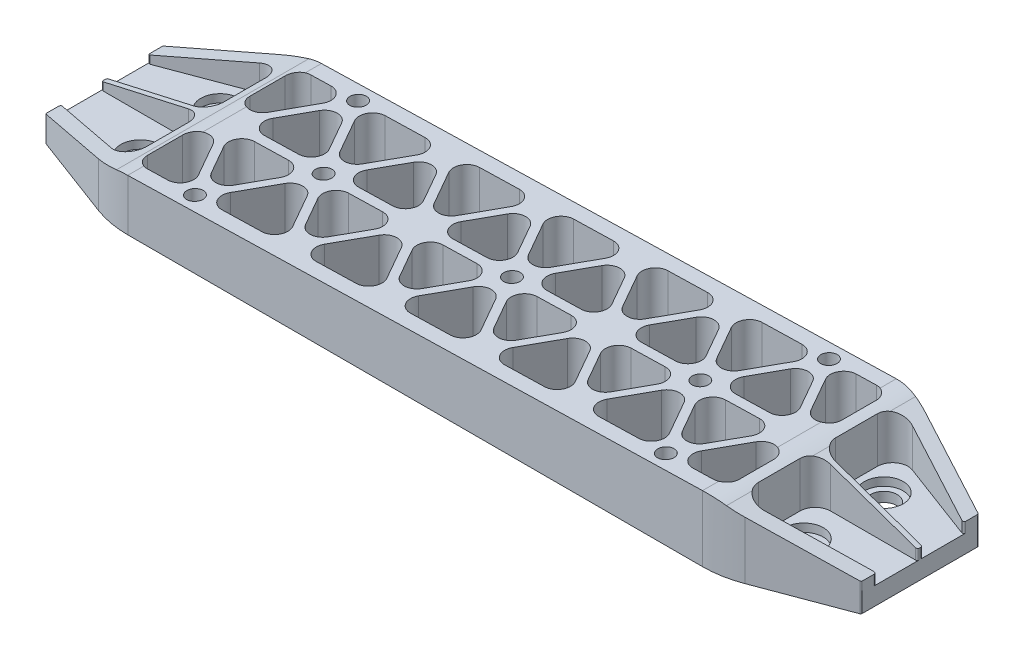
SolidWorks part; units mm, degrees
ref_plane "Front Plane" through (0, 0, 0) normal (0, 0, 1) x (1, 0, 0)
ref_plane "Top Plane" through (0, 0, 0) normal (0, 1, 0) x (1, 0, 0)
ref_plane "Right Plane" through (0, 0, 0) normal (1, 0, 0) x (0, 0, -1)
sketch "Sketch1" plane through (0, 0, 0) normal (0, 1, 0) x (1, 0, 0)
  line L0 (25.4, 0) -> (177.8, 0)
  line L1 (177.8, 0) -> (203.2, -9.525)
  line L2 (203.2, -9.525) -> (203.2, -38.735)
  line L3 (203.2, -38.735) -> (177.8, -48.26)
  line L4 (177.8, -48.26) -> (25.4, -48.26)
  line L5 (25.4, -48.26) -> (0, -38.735)
  line L6 (0, -38.735) -> (0, -9.525)
  line L7 (0, -9.525) -> (25.4, 0)
  line L8 (0, -9.525) -> (203.2, -9.525) construction
  line L9 (25.4, 0) -> (25.4, -48.26) construction
  dimension "D1" = 25.4
  dimension "D2" = 9.525
  dimension "D3" = 177.8
  dimension "D4" = 203.2
  dimension "D5" = 38.735
  dimension "D6" = 48.26
extrude "Boss-Extrude1" add sketch "Sketch1" against normal blind 17.1704
sketch "Sketch2" plane through (0, -17.1704, 0) normal (0, -1, 0) x (1, 0, 0)
  line L0 (0, 24.13) -> (203.2, 24.13) construction
  line L1 (0, 9.525) -> (0, 38.735) construction
  line L2 (203.2, 38.735) -> (203.2, 9.525) construction
  circle A0 centre (54.6608, 24.13) radius 3.4925
  circle A1 centre (101.6, 24.13) radius 3.4925
  circle A2 centre (148.5392, 24.13) radius 3.4925
  dimension "D2" = 6.985
  dimension "D1" = 24.13
  dimension "D3" = 54.6608
  dimension "D4" = 101.6
  dimension "D5" = 148.5392
extrude "Boss-Extrude2" add sketch "Sketch2" along normal blind 5.08
fillet "Fillet1" radius 25.4 4 edges at (177.8, -8.5852, 48.26) (25.4, -8.5852, 48.26) (177.8, -8.5852, 0) (25.4, -8.5852, 0)
fillet "Fillet2" radius 0.381 4 edges at (203.2, -8.5852, 38.735) (203.2, -8.5852, 9.525) (0, -8.5852, 9.525) (0, -8.5852, 38.735)
sketch "Sketch3" plane through (0, 0, 0) normal (0, 1, 0) x (1, 0, 0)
  line L0 (27.94, -24.13) -> (175.26, -24.13) construction
  line L1 (27.94, -3.81) -> (175.26, -3.81) construction
  line L2 (27.94, -3.81) -> (27.94, -44.45) construction
  line L3 (27.94, -44.45) -> (175.26, -44.45) construction
  line L4 (175.26, -3.81) -> (175.26, -44.45) construction
  line L5 (42.929, -3.81) -> (66.3926, -44.45) construction
  line L6 (78.1243, -24.13) -> (66.3926, -3.81) construction
  line L7 (66.3926, -3.81) -> (42.929, -3.81) construction
  line L8 (42.929, -3.81) -> (31.1973, -24.13) construction
  line L9 (31.1973, -24.13) -> (42.929, -44.45) construction
  line L10 (42.929, -44.45) -> (66.3926, -44.45) construction
  line L11 (66.3926, -44.45) -> (78.1243, -24.13) construction
  line L12 (125.0513, -24.13) -> (113.3196, -3.81) construction
  line L13 (113.3196, -3.81) -> (89.8561, -3.81) construction
  line L14 (89.8561, -3.81) -> (78.1243, -24.13) construction
  line L15 (78.1243, -24.13) -> (89.8561, -44.45) construction
  line L16 (89.8561, -44.45) -> (113.3196, -44.45) construction
  line L17 (113.3196, -44.45) -> (125.0513, -24.13) construction
  line L18 (160.2466, -3.81) -> (136.7831, -3.81) construction
  line L19 (136.7831, -3.81) -> (125.0513, -24.13) construction
  line L20 (125.0513, -24.13) -> (136.7831, -44.45) construction
  line L21 (136.7831, -44.45) -> (160.2466, -44.45) construction
  line L22 (160.2466, -44.45) -> (171.9784, -24.13) construction
  line L23 (171.9784, -24.13) -> (160.2466, -3.81) construction
  line L24 (42.929, -44.45) -> (66.3926, -3.81) construction
  line L28 (57.4544, -31.0007) -> (62.4258, -39.6113)
  line L29 (59.6321, -44.45) -> (49.6895, -44.45)
  line L30 (46.8958, -39.6113) -> (51.8672, -31.0007)
  line L31 (38.6909, -25.4) -> (47.1671, -25.4)
  line L32 (49.9608, -30.2387) -> (45.7227, -37.5793)
  line L33 (40.1354, -37.5793) -> (35.8973, -30.2387)
  line L34 (40.1354, -10.6807) -> (35.8973, -18.0213)
  line L35 (49.9608, -18.0213) -> (45.7227, -10.6807)
  line L36 (38.6909, -22.86) -> (47.1671, -22.86)
  line L37 (46.8958, -8.6487) -> (51.8672, -17.2593)
  line L38 (59.6321, -3.81) -> (49.6895, -3.81)
  line L39 (57.4544, -17.2593) -> (62.4258, -8.6487)
  line L40 (63.605, -37.5793) -> (59.3669, -30.2387)
  line L41 (62.1605, -25.4) -> (70.6367, -25.4)
  line L42 (70.3654, -39.6113) -> (75.3368, -31.0007)
  line L43 (73.4304, -30.2387) -> (69.1923, -37.5793)
  line L44 (80.924, -31.0007) -> (85.8954, -39.6113)
  line L45 (83.1017, -44.45) -> (73.1591, -44.45)
  line L46 (70.3654, -8.6487) -> (75.3368, -17.2593)
  line L47 (83.1017, -3.81) -> (73.1591, -3.81)
  line L48 (80.924, -17.2593) -> (85.8954, -8.6487)
  line L49 (63.605, -10.6807) -> (59.3669, -18.0213)
  line L50 (73.4304, -18.0213) -> (69.1923, -10.6807)
  line L51 (62.1605, -22.86) -> (70.6367, -22.86)
  line L52 (87.0746, -37.5793) -> (82.8365, -30.2387)
  line L53 (85.6301, -25.4) -> (94.1063, -25.4)
  line L54 (93.835, -39.6113) -> (98.8064, -31.0007)
  line L55 (96.9, -30.2387) -> (92.6619, -37.5793)
  line L56 (104.3936, -31.0007) -> (109.365, -39.6113)
  line L57 (106.5713, -44.45) -> (96.6287, -44.45)
  line L58 (93.835, -8.6487) -> (98.8064, -17.2593)
  line L59 (106.5713, -3.81) -> (96.6287, -3.81)
  line L60 (104.3936, -17.2593) -> (109.365, -8.6487)
  line L61 (87.0746, -10.6807) -> (82.8365, -18.0213)
  line L62 (96.9, -18.0213) -> (92.6619, -10.6807)
  line L63 (85.6301, -22.86) -> (94.1063, -22.86)
  line L64 (110.5442, -37.5793) -> (106.3061, -30.2387)
  line L65 (109.0997, -25.4) -> (117.5759, -25.4)
  line L66 (117.3046, -39.6113) -> (122.276, -31.0007)
  line L67 (120.3696, -30.2387) -> (116.1315, -37.5793)
  line L68 (127.8632, -31.0007) -> (132.8346, -39.6113)
  line L69 (130.0409, -44.45) -> (120.0983, -44.45)
  line L70 (117.3046, -8.6487) -> (122.276, -17.2593)
  line L71 (130.0409, -3.81) -> (120.0983, -3.81)
  line L72 (127.8632, -17.2593) -> (132.8346, -8.6487)
  line L73 (110.5442, -10.6807) -> (106.3061, -18.0213)
  line L74 (120.3696, -18.0213) -> (116.1315, -10.6807)
  line L75 (109.0997, -22.86) -> (117.5759, -22.86)
  line L76 (134.0138, -37.5793) -> (129.7757, -30.2387)
  line L77 (132.5693, -25.4) -> (141.0455, -25.4)
  line L78 (140.7742, -39.6113) -> (145.7456, -31.0007)
  line L79 (143.8392, -30.2387) -> (139.6011, -37.5793)
  line L80 (151.3328, -31.0007) -> (156.3042, -39.6113)
  line L81 (153.5105, -44.45) -> (143.5679, -44.45)
  line L82 (140.7742, -8.6487) -> (145.7456, -17.2593)
  line L83 (153.5105, -3.81) -> (143.5679, -3.81)
  line L84 (151.3328, -17.2593) -> (156.3042, -8.6487)
  line L85 (134.0138, -10.6807) -> (129.7757, -18.0213)
  line L86 (143.8392, -18.0213) -> (139.6011, -10.6807)
  line L87 (132.5693, -22.86) -> (141.0455, -22.86)
  line L88 (157.4834, -37.5793) -> (153.2453, -30.2387)
  line L89 (156.0389, -25.4) -> (164.5151, -25.4)
  line L90 (164.2438, -39.6113) -> (169.2406, -30.9567)
  line L91 (167.3088, -30.2387) -> (163.0707, -37.5793)
  line L94 (164.2438, -8.6487) -> (169.2406, -17.3033)
  line L97 (157.4834, -10.6807) -> (153.2453, -18.0213)
  line L98 (167.3088, -18.0213) -> (163.0707, -10.6807)
  line L99 (156.0389, -22.86) -> (164.5151, -22.86)
  line L101 (33.9594, -30.9567) -> (38.9562, -39.6113)
  line L105 (33.9594, -17.3033) -> (38.9562, -8.6487)
  line L106 (23.4262, -39.6113) -> (28.3976, -31.0007) [skipped]
  line L107 (23.4262, -8.6487) -> (28.3976, -17.2593) [skipped]
  line L108 (36.1625, -3.81) -> (26.2199, -3.81) [skipped]
  line L109 (36.1625, -44.45) -> (26.2199, -44.45) [skipped]
  line L110 (174.8024, -17.2593) -> (179.7738, -8.6487) [skipped]
  line L111 (176.9801, -3.81) -> (167.0375, -3.81) [skipped]
  line L112 (174.8024, -31.0007) -> (179.7738, -39.6113) [skipped]
  line L113 (176.9801, -44.45) -> (167.0375, -44.45) [skipped]
  line L114 (27.94, -7.0358) -> (27.94, -15.6904)
  line L115 (27.94, -32.5696) -> (27.94, -41.2242)
  line L116 (175.26, -32.5696) -> (175.26, -41.2242)
  line L117 (175.26, -7.0358) -> (175.26, -15.6904)
  line L118 (167.0375, -44.45) -> (172.0342, -44.45)
  line L119 (167.0375, -3.81) -> (172.0342, -3.81)
  line L120 (36.1625, -3.81) -> (31.1658, -3.81)
  line L121 (36.1625, -44.45) -> (31.1658, -44.45)
  line L122 (203.2, -38.471) -> (203.2, -9.789) construction
  line L123 (173.1941, 0) -> (30.0059, 0) construction
  circle A0 centre (54.6608, -24.13) radius 20.32 construction
  circle A1 centre (101.5878, -24.13) radius 20.32 construction
  circle A2 centre (148.5149, -24.13) radius 20.32 construction
  circle A3 centre (42.929, -3.81) radius 2.0193
  circle A4 centre (42.929, -44.45) radius 2.0193
  circle A5 centre (54.6608, -24.13) radius 2.0193
  circle A6 centre (101.5878, -24.13) radius 2.0193
  circle A7 centre (148.5149, -24.13) radius 2.0193
  circle A8 centre (160.2466, -3.81) radius 2.0193
  circle A9 centre (160.2466, -44.45) radius 2.0193
  arc A10 (51.8672, -31.0007) -> (57.4544, -31.0007) centre (54.6608, -32.6136) cw
  arc A11 (59.6321, -44.45) -> (62.4258, -39.6113) centre (59.6321, -41.2242) ccw
  arc A12 (49.6895, -44.45) -> (46.8958, -39.6113) centre (49.6895, -41.2242) cw
  arc A13 (45.7227, -37.5793) -> (40.1354, -37.5793) centre (42.929, -35.9664) cw
  arc A14 (49.9608, -30.2387) -> (47.1671, -25.4) centre (47.1671, -28.6258) ccw
  arc A15 (35.8973, -30.2387) -> (38.6909, -25.4) centre (38.6909, -28.6258) cw
  arc A16 (35.8973, -18.0213) -> (38.6909, -22.86) centre (38.6909, -19.6342) ccw
  arc A17 (49.9608, -18.0213) -> (47.1671, -22.86) centre (47.1671, -19.6342) cw
  arc A18 (45.7227, -10.6807) -> (40.1354, -10.6807) centre (42.929, -12.2936) ccw
  arc A19 (49.6895, -3.81) -> (46.8958, -8.6487) centre (49.6895, -7.0358) ccw
  arc A20 (59.6321, -3.81) -> (62.4258, -8.6487) centre (59.6321, -7.0358) cw
  arc A21 (51.8672, -17.2593) -> (57.4544, -17.2593) centre (54.6608, -15.6464) ccw
  arc A22 (59.3669, -30.2387) -> (62.1605, -25.4) centre (62.1605, -28.6258) cw
  arc A23 (73.1591, -44.45) -> (70.3654, -39.6113) centre (73.1591, -41.2242) cw
  arc A24 (69.1923, -37.5793) -> (63.605, -37.5793) centre (66.3986, -35.9664) cw
  arc A25 (73.4304, -30.2387) -> (70.6367, -25.4) centre (70.6367, -28.6258) ccw
  arc A26 (75.3368, -31.0007) -> (80.924, -31.0007) centre (78.1304, -32.6136) cw
  arc A27 (83.1017, -44.45) -> (85.8954, -39.6113) centre (83.1017, -41.2242) ccw
  arc A28 (73.1591, -3.81) -> (70.3654, -8.6487) centre (73.1591, -7.0358) ccw
  arc A29 (83.1017, -3.81) -> (85.8954, -8.6487) centre (83.1017, -7.0358) cw
  arc A30 (75.3368, -17.2593) -> (80.924, -17.2593) centre (78.1304, -15.6464) ccw
  arc A31 (73.4304, -18.0213) -> (70.6367, -22.86) centre (70.6367, -19.6342) cw
  arc A32 (69.1923, -10.6807) -> (63.605, -10.6807) centre (66.3986, -12.2936) ccw
  arc A33 (59.3669, -18.0213) -> (62.1605, -22.86) centre (62.1605, -19.6342) ccw
  arc A34 (82.8365, -30.2387) -> (85.6301, -25.4) centre (85.6301, -28.6258) cw
  arc A35 (96.6287, -44.45) -> (93.835, -39.6113) centre (96.6287, -41.2242) cw
  arc A36 (92.6619, -37.5793) -> (87.0746, -37.5793) centre (89.8682, -35.9664) cw
  arc A37 (96.9, -30.2387) -> (94.1063, -25.4) centre (94.1063, -28.6258) ccw
  arc A38 (98.8064, -31.0007) -> (104.3936, -31.0007) centre (101.6, -32.6136) cw
  arc A39 (106.5713, -44.45) -> (109.365, -39.6113) centre (106.5713, -41.2242) ccw
  arc A40 (96.6287, -3.81) -> (93.835, -8.6487) centre (96.6287, -7.0358) ccw
  arc A41 (106.5713, -3.81) -> (109.365, -8.6487) centre (106.5713, -7.0358) cw
  arc A42 (98.8064, -17.2593) -> (104.3936, -17.2593) centre (101.6, -15.6464) ccw
  arc A43 (96.9, -18.0213) -> (94.1063, -22.86) centre (94.1063, -19.6342) cw
  arc A44 (92.6619, -10.6807) -> (87.0746, -10.6807) centre (89.8682, -12.2936) ccw
  arc A45 (82.8365, -18.0213) -> (85.6301, -22.86) centre (85.6301, -19.6342) ccw
  arc A46 (106.3061, -30.2387) -> (109.0997, -25.4) centre (109.0997, -28.6258) cw
  arc A47 (120.0983, -44.45) -> (117.3046, -39.6113) centre (120.0983, -41.2242) cw
  arc A48 (116.1315, -37.5793) -> (110.5442, -37.5793) centre (113.3378, -35.9664) cw
  arc A49 (120.3696, -30.2387) -> (117.5759, -25.4) centre (117.5759, -28.6258) ccw
  arc A50 (122.276, -31.0007) -> (127.8632, -31.0007) centre (125.0696, -32.6136) cw
  arc A51 (130.0409, -44.45) -> (132.8346, -39.6113) centre (130.0409, -41.2242) ccw
  arc A52 (120.0983, -3.81) -> (117.3046, -8.6487) centre (120.0983, -7.0358) ccw
  arc A53 (130.0409, -3.81) -> (132.8346, -8.6487) centre (130.0409, -7.0358) cw
  arc A54 (122.276, -17.2593) -> (127.8632, -17.2593) centre (125.0696, -15.6464) ccw
  arc A55 (120.3696, -18.0213) -> (117.5759, -22.86) centre (117.5759, -19.6342) cw
  arc A56 (116.1315, -10.6807) -> (110.5442, -10.6807) centre (113.3378, -12.2936) ccw
  arc A57 (106.3061, -18.0213) -> (109.0997, -22.86) centre (109.0997, -19.6342) ccw
  arc A58 (129.7757, -30.2387) -> (132.5693, -25.4) centre (132.5693, -28.6258) cw
  arc A59 (143.5679, -44.45) -> (140.7742, -39.6113) centre (143.5679, -41.2242) cw
  arc A60 (139.6011, -37.5793) -> (134.0138, -37.5793) centre (136.8074, -35.9664) cw
  arc A61 (143.8392, -30.2387) -> (141.0455, -25.4) centre (141.0455, -28.6258) ccw
  arc A62 (145.7456, -31.0007) -> (151.3328, -31.0007) centre (148.5392, -32.6136) cw
  arc A63 (153.5105, -44.45) -> (156.3042, -39.6113) centre (153.5105, -41.2242) ccw
  arc A64 (143.5679, -3.81) -> (140.7742, -8.6487) centre (143.5679, -7.0358) ccw
  arc A65 (153.5105, -3.81) -> (156.3042, -8.6487) centre (153.5105, -7.0358) cw
  arc A66 (145.7456, -17.2593) -> (151.3328, -17.2593) centre (148.5392, -15.6464) ccw
  arc A67 (143.8392, -18.0213) -> (141.0455, -22.86) centre (141.0455, -19.6342) cw
  arc A68 (139.6011, -10.6807) -> (134.0138, -10.6807) centre (136.8074, -12.2936) ccw
  arc A69 (129.7757, -18.0213) -> (132.5693, -22.86) centre (132.5693, -19.6342) ccw
  arc A70 (153.2453, -30.2387) -> (156.0389, -25.4) centre (156.0389, -28.6258) cw
  arc A71 (167.0375, -44.45) -> (164.2438, -39.6113) centre (167.0375, -41.2242) cw
  arc A72 (163.0707, -37.5793) -> (157.4834, -37.5793) centre (160.277, -35.9664) cw
  arc A73 (167.3088, -30.2387) -> (164.5151, -25.4) centre (164.5151, -28.6258) ccw
  arc A76 (167.0375, -3.81) -> (164.2438, -8.6487) centre (167.0375, -7.0358) ccw
  arc A79 (167.3088, -18.0213) -> (164.5151, -22.86) centre (164.5151, -19.6342) cw
  arc A80 (163.0707, -10.6807) -> (157.4834, -10.6807) centre (160.277, -12.2936) ccw
  arc A81 (153.2453, -18.0213) -> (156.0389, -22.86) centre (156.0389, -19.6342) ccw
  arc A84 (36.1625, -44.45) -> (38.9562, -39.6113) centre (36.1625, -41.2242) ccw
  arc A86 (36.1625, -3.81) -> (38.9562, -8.6487) centre (36.1625, -7.0358) cw
  arc A88 (26.2199, -44.45) -> (23.4262, -39.6113) centre (26.2199, -41.2242) cw [skipped]
  arc A89 (26.2199, -3.81) -> (23.4262, -8.6487) centre (26.2199, -7.0358) ccw [skipped]
  arc A90 (28.3976, -31.0007) -> (33.9848, -31.0007) centre (31.1912, -32.6136) cw [skipped]
  arc A91 (176.9801, -3.81) -> (179.7738, -8.6487) centre (176.9801, -7.0358) cw [skipped]
  arc A92 (176.9801, -44.45) -> (179.7738, -39.6113) centre (176.9801, -41.2242) ccw [skipped]
  arc A93 (169.2152, -31.0007) -> (174.8024, -31.0007) centre (172.0088, -32.6136) cw [skipped]
  arc A94 (169.2152, -17.2593) -> (174.8024, -17.2593) centre (172.0088, -15.6464) ccw [skipped]
  arc A95 (28.3976, -17.2593) -> (33.9848, -17.2593) centre (31.1912, -15.6464) ccw [skipped]
  arc A96 (172.0342, -3.81) -> (175.26, -7.0358) centre (172.0342, -7.0358) cw
  arc A97 (175.26, -15.6904) -> (169.2406, -17.3033) centre (172.0342, -15.6904) cw
  arc A98 (169.2406, -30.9567) -> (175.26, -32.5696) centre (172.0342, -32.5696) cw
  arc A99 (172.0342, -44.45) -> (175.26, -41.2242) centre (172.0342, -41.2242) ccw
  arc A100 (27.94, -41.2242) -> (31.1658, -44.45) centre (31.1658, -41.2242) ccw
  arc A101 (27.94, -32.5696) -> (33.9594, -30.9567) centre (31.1658, -32.5696) cw
  arc A102 (27.94, -15.6904) -> (33.9594, -17.3033) centre (31.1658, -15.6904) ccw
  arc A103 (27.94, -7.0358) -> (31.1658, -3.81) centre (31.1658, -7.0358) cw
  point P47 (65.2194, -44.45)
  point P50 (44.1022, -44.45)
  dimension "D6" = 4.0386
  dimension "D7" = 1.016
  dimension "D9" = 2.032
  dimension "D12" = 3.2258
  dimension "D15" = 3.2258
  dimension "D1" = 3.81
  dimension "D2" = 44.45
  dimension "D3" = 27.94
  dimension "D4" = 175.26
  dimension "D5" = 54.6608
  dimension "D8" = 1.016
  dimension "D10" = 1.27
  dimension "D11" = 1.016
  dimension "D13" = 6
  dimension "D14" = 2
extrude "Cut-Extrude1" cut sketch "Sketch3" against normal up to next
sketch "Sketch4" plane through (0, 0, 0) normal (0, 1, 0) x (1, 0, 0)
  line L0 (0, -13.3228) -> (20.2522, -5.7282)
  line L1 (0, -9.789) -> (0, -38.471) construction
  line L2 (25.4, -9.2956) -> (25.4, -19.685)
  line L3 (21.59, -23.495) -> (0, -23.495)
  line L4 (0, -23.495) -> (0, -13.3228)
  line L5 (203.2, -13.3228) -> (182.9478, -5.7282)
  line L6 (203.2, -38.471) -> (203.2, -9.789) construction
  line L7 (177.8, -9.2956) -> (177.8, -19.685)
  line L8 (181.61, -23.495) -> (203.2, -23.495)
  line L9 (203.2, -23.495) -> (203.2, -13.3228)
  line L10 (0, -24.13) -> (203.2, -24.13) construction
  line L11 (27.94, -7.0358) -> (27.94, -15.6904) construction
  line L12 (175.26, -15.6904) -> (175.26, -7.0358) construction
  line L13 (21.0874, -1.6172) -> (0.2472, -9.4323) construction
  line L14 (202.9528, -9.4323) -> (182.1126, -1.6172) construction
  line L15 (181.61, -24.765) -> (203.2, -24.765)
  line L16 (177.8, -38.9644) -> (177.8, -28.575)
  line L17 (203.2, -34.9372) -> (182.9478, -42.5318)
  line L18 (203.2, -24.765) -> (203.2, -34.9372)
  line L19 (21.59, -24.765) -> (0, -24.765)
  line L20 (25.4, -38.9644) -> (25.4, -28.575)
  line L21 (0, -34.9372) -> (20.2522, -42.5318)
  line L22 (0, -24.765) -> (0, -34.9372)
  arc A0 (181.61, -23.495) -> (177.8, -19.685) centre (181.61, -19.685) cw
  arc A1 (182.9478, -5.7282) -> (177.8, -9.2956) centre (181.61, -9.2956) ccw
  arc A2 (25.4, -19.685) -> (21.59, -23.495) centre (21.59, -19.685) cw
  arc A3 (25.4, -9.2956) -> (20.2522, -5.7282) centre (21.59, -9.2956) ccw
  arc A4 (181.61, -24.765) -> (177.8, -28.575) centre (181.61, -28.575) ccw
  arc A5 (182.9478, -42.5318) -> (177.8, -38.9644) centre (181.61, -38.9644) cw
  arc A6 (25.4, -28.575) -> (21.59, -24.765) centre (21.59, -28.575) ccw
  arc A7 (25.4, -38.9644) -> (20.2522, -42.5318) centre (21.59, -38.9644) cw
  dimension "D3" = 3.81
  dimension "D1" = 1.27
  dimension "D2" = 1.27
  dimension "D4" = 2.54
  dimension "D5" = 2.54
  dimension "D6" = 3.556
  dimension "D7" = 3.556
extrude "Cut-Extrude2" cut sketch "Sketch4" against normal blind 12.7
sketch "Sketch6" plane through (0, -12.7, 0) normal (0, 1, 0) x (1, 0, 0)
  line L1 (18.923, -14.1732) -> (184.277, -14.1732) construction
  line L2 (18.923, -14.1732) -> (18.923, -34.0868) construction
  line L3 (18.923, -34.0868) -> (184.277, -34.0868) construction
  line L4 (184.277, -14.1732) -> (184.277, -34.0868) construction
  circle A1 centre (18.923, -14.1732) radius 3.302
  circle A2 centre (184.277, -14.1732) radius 3.302
  circle A3 centre (184.277, -34.0868) radius 3.302
  circle A4 centre (18.923, -34.0868) radius 3.302
  dimension "D5" = 6.604
  dimension "D1" = 18.923
  dimension "D2" = 184.277
  dimension "D3" = 34.0868
  dimension "D4" = 14.1732
extrude "Cut-Extrude3" cut sketch "Sketch6" against normal up to next
sketch "Sketch7" plane through (0, -12.7, 0) normal (0, 1, 0) x (1, 0, 0)
  circle A0 centre (18.923, -14.1732) radius 4.826
  circle A1 centre (18.923, -34.0868) radius 4.826
  circle A2 centre (184.277, -34.0868) radius 4.826
  circle A3 centre (184.277, -14.1732) radius 4.826
  dimension "D1" = 9.652
extrude "Cut-Extrude4" cut sketch "Sketch7" against normal blind 2.032
fillet "Fillet3" radius 0.381 8 edges at (0, -6.35, 34.9372) (0, -6.35, 24.765) (0, -6.35, 23.495) (0, -6.35, 13.3228) (203.2, -6.35, 13.3228) (203.2, -6.35, 23.495) (203.2, -6.35, 24.765) (203.2, -6.35, 34.9372)
sketch "Sketch8" plane through (0, 0, 48.26) normal (0, 0, 1) x (1, 0, 0)
  line L0 (0, 0) -> (203.2, 0)
  line L1 (0, 0) -> (0, -10.795)
  line L3 (0, -10.795) -> (27.0248, -4.6988)
  line L4 (29.9974, -4.3301) -> (173.2026, -0.7499)
  line L5 (178.5948, -1.5927) -> (203.2, -10.16)
  line L7 (203.2, -10.16) -> (203.2, 0)
  line L9 (0.2472, 0) -> (21.0874, 0) construction
  line L10 (203.2, 0) -> (0, -5.08) construction
  arc A0 (29.9974, -4.3301) -> (27.0248, -4.6988) centre (30.3783, -19.5653) ccw
  arc A1 (178.5948, -1.5927) -> (173.2026, -0.7499) centre (173.5835, -15.9852) ccw
  dimension "D4" = 15.24
  dimension "D1" = 10.795
  dimension "D2" = 5.08
  dimension "D3" = 10.16
  dimension "D5" = 29.9974
  dimension "D6" = 173.2026
extrude "Cut-Extrude5" cut sketch "Sketch8" against normal up to surface (48.26 mm away) up to face at (101.6, -8.5852, 0)
